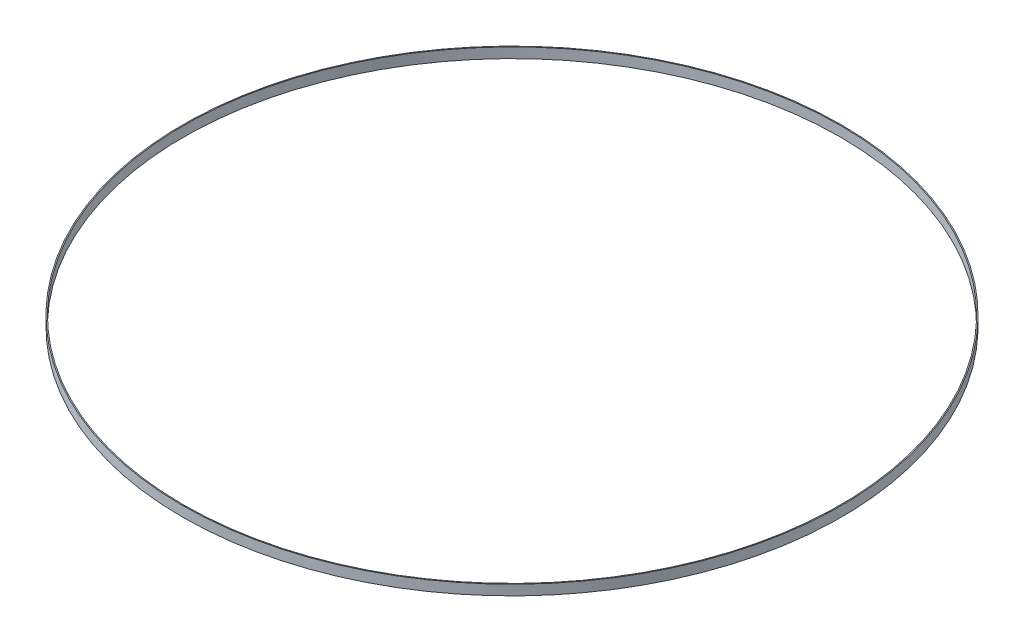
SolidWorks part; units mm, degrees
material "6061-T6 (SS)"
ref_plane "Front Plane" through (0, 0, 0) normal (0, 0, 1) x (1, 0, 0)
ref_plane "Top Plane" through (0, 0, 0) normal (0, 1, 0) x (1, 0, 0)
ref_plane "Right Plane" through (0, 0, 0) normal (1, 0, 0) x (0, 0, -1)
sketch "Sketch1" plane through (0, 0, 0) normal (0, 1, 0) x (1, 0, 0)
  circle A0 centre (0, 0) radius 82.55
  circle A1 centre (0, 0) radius 82.296
  dimension "D1" = 165.1
  dimension "D2" = 0.254
extrude "Boss-Extrude1" add sketch "Sketch1" along normal blind 2.54
